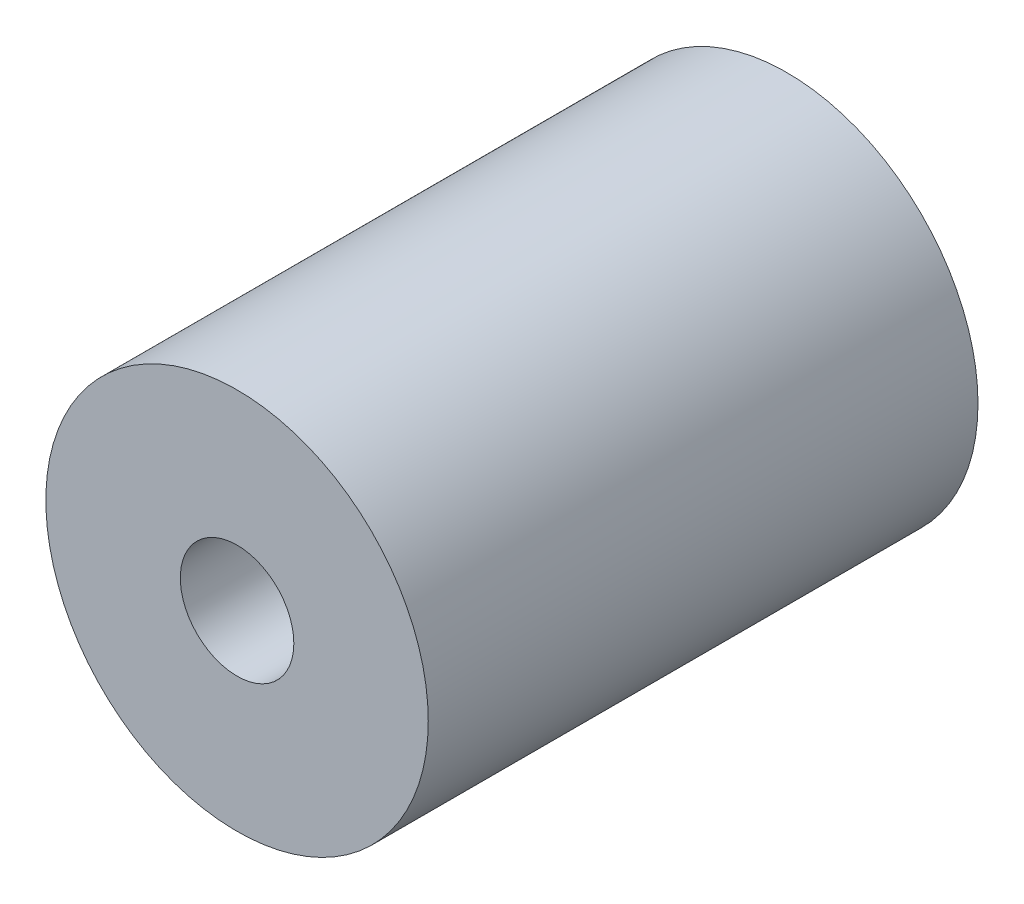
SolidWorks part; units mm, degrees
ref_plane "Front Plane" through (0, 0, 0) normal (0, 0, 1) x (1, 0, 0)
ref_plane "Top Plane" through (0, 0, 0) normal (0, 1, 0) x (1, 0, 0)
ref_plane "Right Plane" through (0, 0, 0) normal (1, 0, 0) x (0, 0, -1)
sketch "Sketch1" plane through (0, 0, 0) normal (0, 0, 1) x (1, 0, 0)
  circle A0 centre (0, 0) radius 2.375
  circle A1 centre (0, 0) radius 8
  dimension "D1" = 4.75
  dimension "D2" = 16
extrude "Boss-Extrude1" add sketch "Sketch1" along normal blind 23
